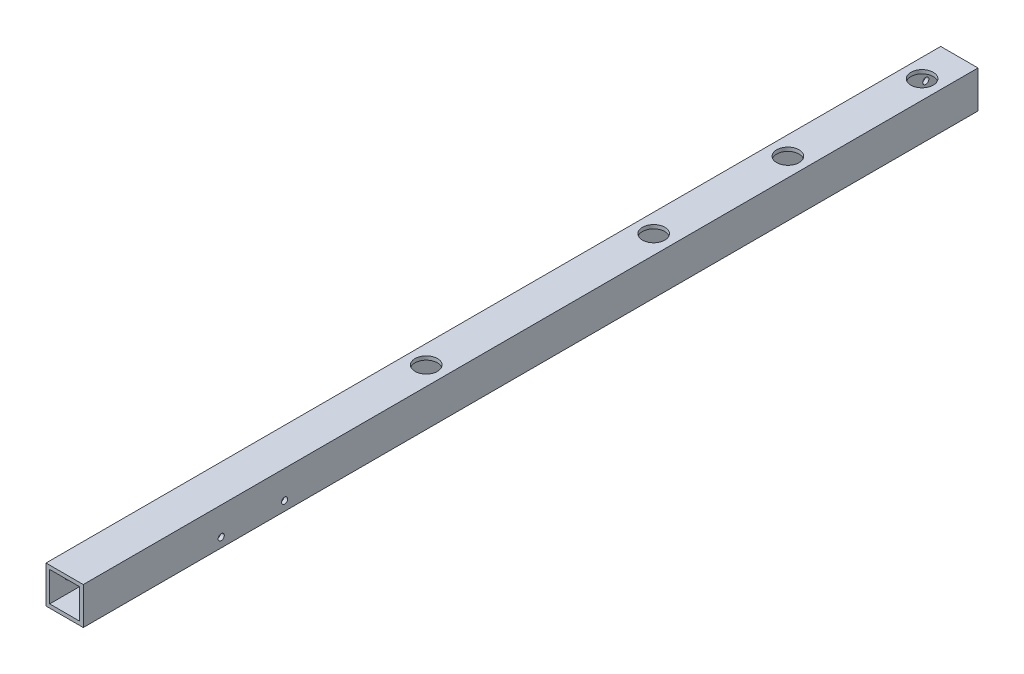
SolidWorks part; units mm, degrees
ref_plane "正面" through (0, 0, 0) normal (0, 0, 1) x (1, 0, 0)
ref_plane "平面" through (0, 0, 0) normal (0, 1, 0) x (1, 0, 0)
ref_plane "右側面" through (0, 0, 0) normal (1, 0, 0) x (0, 0, -1)
sketch "ｽｹｯﾁ1" plane through (0, 0, 0) normal (0, 0, 1) x (1, 0, 0)
  line L1 (-10, 10) -> (10, 10)
  line L2 (-10, 10) -> (-10, -10)
  line L3 (-10, -10) -> (10, -10)
  line L4 (10, 10) -> (10, -10)
  line L5 (-10, 10) -> (10, -10) construction
  line L6 (-10, -10) -> (10, 10) construction
  line L7 (-8, 8) -> (8, 8)
  line L8 (-8, 8) -> (-8, -8)
  line L9 (-8, -8) -> (8, -8)
  line L10 (8, 8) -> (8, -8)
  line L11 (-8, 8) -> (8, -8) construction
  line L12 (-8, -8) -> (8, 8) construction
  point P0 (0, 0)
  point P6 (0, 0)
  dimension "D1" = 20
  dimension "D2" = 20
  dimension "D3" = 16
  dimension "D4" = 16
extrude "ﾎﾞｽ - 押し出し1" add sketch "ｽｹｯﾁ1" along normal blind 560
sketch "ｽｹｯﾁ3" plane through (10, 0, 0) normal (1, 0, 0) x (0, 0, -1)
  line L0 (-560, 0) -> (-530, 0)
  line L1 (-560, -10) -> (-560, 10) construction
  line L2 (-530, 0) -> (-30, 0)
  circle A0 centre (-530, 0) radius 2.2
  circle A1 centre (-30, 0) radius 2.2
  dimension "D2" = 4.4
  dimension "D4" = 4.4
  dimension "D1" = 30
  dimension "D3" = 500
extrude "ｶｯﾄ - 押し出し2" cut sketch "ｽｹｯﾁ3" against normal blind 560
sketch "ｽｹｯﾁ4" plane through (0, 10, 0) normal (0, 1, 0) x (1, 0, 0)
  line L0 (0, -560) -> (0, -550)
  line L1 (10, -560) -> (-10, -560) construction
  line L2 (0, -550) -> (0, -10)
  circle A0 centre (0, -550) radius 2.2
  circle A1 centre (0, -10) radius 2.2
  dimension "D2" = 4.4
  dimension "D4" = 4.4
  dimension "D1" = 10
  dimension "D3" = 540
extrude "ｶｯﾄ - 押し出し3" cut sketch "ｽｹｯﾁ4" against normal blind 560
sketch "ｽｹｯﾁ6" plane through (0, 10, 0) normal (0, 1, 0) x (1, 0, 0)
  line L0 (0, -10) -> (0, -57)
  line L1 (0, -57) -> (0, -122)
  line L2 (0, -122) -> (0, -187)
  circle A0 centre (0, -57) radius 2.2
  circle A1 centre (0, -122) radius 2.2
  circle A2 centre (0, -187) radius 2.2
  dimension "D2" = 4.4
  dimension "D5" = 4.4
  dimension "D6" = 4.4
  dimension "D1" = 47
  dimension "D3" = 65
  dimension "D4" = 65
sketch "ｽｹｯﾁ7" plane through (0, 0, 0) normal (0, 0, -1) x (-1, 0, 0)
  line L1 (20.5547, -20.8177) -> (-20.5547, -20.8177)
  line L2 (20.5547, -20.8177) -> (20.5547, 20.8177)
  line L3 (20.5547, 20.8177) -> (-20.5547, 20.8177)
  line L4 (-20.5547, -20.8177) -> (-20.5547, 20.8177)
  line L5 (20.5547, -20.8177) -> (-20.5547, 20.8177) construction
  line L6 (20.5547, 20.8177) -> (-20.5547, -20.8177) construction
  point P0 (0, 0)
extrude "ｶｯﾄ - 押し出し7" cut sketch "ｽｹｯﾁ7" against normal blind 40
sketch "ｽｹｯﾁ8" plane through (0, 0, 560) normal (0, 0, 1) x (1, 0, 0)
  line L1 (26.7152, 16.8398) -> (-26.7152, 16.8398)
  line L2 (26.7152, 16.8398) -> (26.7152, -16.8398)
  line L3 (26.7152, -16.8398) -> (-26.7152, -16.8398)
  line L4 (-26.7152, 16.8398) -> (-26.7152, -16.8398)
  line L5 (26.7152, 16.8398) -> (-26.7152, -16.8398) construction
  line L6 (26.7152, -16.8398) -> (-26.7152, 16.8398) construction
  point P0 (0, 0)
extrude "ｶｯﾄ - 押し出し8" cut sketch "ｽｹｯﾁ8" against normal blind 40
sketch "ｽｹｯﾁ9" plane through (-10, 0, 0) normal (-1, 0, 0) x (0, 0, 1)
  line L0 (510, 0) -> (520, 0)
  line L2 (520, -10) -> (520, 10) construction
  line L3 (510, 0) -> (490, 0)
  circle A0 centre (510, 0) radius 1
  circle A1 centre (490, 0) radius 1
  dimension "D2" = 2
  dimension "D4" = 2
  dimension "D1" = 10
  dimension "D3" = 20
extrude "ｶｯﾄ - 押し出し9" cut sketch "ｽｹｯﾁ9" against normal blind 10
sketch "ｽｹｯﾁ10" plane through (-10, 0, 0) normal (-1, 0, 0) x (0, 0, 1)
  line L0 (40, 0) -> (50, 0)
  line L1 (40, -10) -> (40, 10) construction
  line L2 (50, 0) -> (70, 0)
  circle A0 centre (50, 0) radius 1
  circle A1 centre (70, 0) radius 1
  dimension "D2" = 2
  dimension "D4" = 2
  dimension "D1" = 10
  dimension "D3" = 20
extrude "ｶｯﾄ - 押し出し10" cut sketch "ｽｹｯﾁ10" against normal blind 10
sketch "ｽｹｯﾁ11" plane through (0, 10, 0) normal (0, 1, 0) x (1, 0, 0)
  line L0 (0, -40) -> (0, -60)
  line L1 (-10, -40) -> (10, -40) construction
  line L2 (0, -60) -> (0, -132)
  line L3 (0, -132) -> (0, -204)
  circle A0 centre (0, -60) radius 2.1
  circle A1 centre (0, -132) radius 2.1
  circle A3 centre (0, -204) radius 2.1
  dimension "D4" = 4.2
  dimension "D5" = 4.2
  dimension "D6" = 4.2
  dimension "D1" = 20
  dimension "D2" = 72
  dimension "D3" = 72
extrude "ｶｯﾄ - 押し出し11" cut sketch "ｽｹｯﾁ11" against normal through all
sketch "ｽｹｯﾁ12" plane through (0, 10, 0) normal (0, 1, 0) x (1, 0, 0)
  circle A0 centre (0, -60) radius 6
  circle A1 centre (0, -132) radius 6
  circle A2 centre (0, -204) radius 6
  dimension "D1" = 12
  dimension "D2" = 12
  dimension "D3" = 12
extrude "ｶｯﾄ - 押し出し12" cut sketch "ｽｹｯﾁ12" against normal blind 10
sketch "ｽｹｯﾁ13" plane through (-10, 0, 0) normal (-1, 0, 0) x (0, 0, 1)
  line L4 (131, 10) -> (131, 5)
  line L5 (520, 10) -> (40, 10) construction
  line L6 (131, 5) -> (114, 5)
  line L7 (131, 5) -> (148, 5)
  circle A2 centre (148, 5) radius 2.1
  circle A3 centre (114, 5) radius 2.1
  dimension "D5" = 4.2
  dimension "D6" = 4.2
  dimension "D1" = 5
  dimension "D2" = 17
  dimension "D3" = 17
sketch "ｽｹｯﾁ14" plane through (-10, 0, 0) normal (-1, 0, 0) x (0, 0, 1)
  line L2 (429, -10) -> (429, -5)
  line L3 (520, -10) -> (40, -10) construction
  line L4 (429, -5) -> (446, -5)
  line L5 (429, -5) -> (412, -5)
  circle A0 centre (446, -5) radius 2.1
  circle A1 centre (412, -5) radius 2.1
  dimension "D4" = 4.2
  dimension "D5" = 4.2
  dimension "D1" = 5
  dimension "D2" = 17
  dimension "D3" = 17
sketch "ｽｹｯﾁ15" plane through (0, 10, 0) normal (0, 1, 0) x (1, 0, 0)
  line L0 (0, -520) -> (0, -326)
  line L1 (-10, -520) -> (10, -520) construction
  circle A0 centre (0, -326) radius 2.1
  dimension "D2" = 4.2
  dimension "D1" = 194
extrude "ｶｯﾄ - 押し出し16" cut sketch "ｽｹｯﾁ15" against normal through all
sketch "ｽｹｯﾁ16" plane through (0, 10, 0) normal (0, 1, 0) x (1, 0, 0)
  circle A0 centre (0, -326) radius 6
  dimension "D1" = 12
extrude "ｶｯﾄ - 押し出し17" cut sketch "ｽｹｯﾁ16" against normal blind 10
hole_wizard "M4x0.7 ねじ穴6" positions "3Dｽｹｯﾁ7" profile "ｽｹｯﾁ23" tap size "M4x0.7" standard "JIS"
sketch3d "3Dｽｹｯﾁ7"
  line L0 (-8, 0, 70) -> (-10, 0, 70) construction
  line L1 (-8, 0, 50) -> (-10, 0, 50) construction
  point P0 (-10, 0, 70)
  point P4 (-10, 0, 50)
sketch "ｽｹｯﾁ23" plane through (-10, 0, 70) normal (0, 1, 0) x (0, 0, 1)
  line L0 (0, 0) -> (0, 12.4914)
  line L1 (0, 12.4914) -> (1.65, 11.5)
  line L2 (1.65, 11.5) -> (1.65, 0)
  line L5 (1.65, 0) -> (0, 0)
  line L10 (0, 12.4914) -> (-1.65, 11.5) construction
  line L11 (0, -6.35) -> (0, 107.95) construction
  dimension "ねじ下穴ﾄﾞﾘﾙ直径" = 3.3
  dimension "ねじ下穴ﾄﾞﾘﾙの深さ" = 11.5
  dimension "ﾄﾞﾘﾙ角度" = 118
cosmetic thread "穴のねじ山12" parameters "D1"=2, "D2"=4
cosmetic thread "穴のねじ山13" parameters "D1"=2, "D2"=4
hole_wizard "M4x0.7 ねじ穴7" positions "3Dｽｹｯﾁ8" profile "ｽｹｯﾁ24" tap size "M4x0.7" standard "JIS"
sketch3d "3Dｽｹｯﾁ8"
  line L0 (-8, 0, 490) -> (-10, 0, 490) construction
  line L1 (-8, 0, 510) -> (-10, 0, 510) construction
  point P0 (-8, 0, 490)
  point P4 (-10, 0, 510)
sketch "ｽｹｯﾁ24" plane through (-8, 0, 490) normal (0, 1, 0) x (0, 0, -1)
  line L0 (0, 0) -> (0, 12.4914)
  line L1 (0, 12.4914) -> (1.65, 11.5)
  line L2 (1.65, 11.5) -> (1.65, 0)
  line L5 (1.65, 0) -> (0, 0)
  line L10 (0, 12.4914) -> (-1.65, 11.5) construction
  line L11 (0, -6.35) -> (0, 107.95) construction
  dimension "ねじ下穴ﾄﾞﾘﾙ直径" = 3.3
  dimension "ねじ下穴ﾄﾞﾘﾙの深さ" = 11.5
  dimension "ﾄﾞﾘﾙ角度" = 118
cosmetic thread "穴のねじ山14" parameters "D1"=2, "D2"=4
cosmetic thread "穴のねじ山15" parameters "D1"=2, "D2"=4
sketch "ｽｹｯﾁ26" plane through (10, 0, 0) normal (1, 0, 0) x (0, 0, -1)
  line L0 (-520, -10) -> (-520, -5)
  line L1 (-520, 10) -> (-520, -10) construction
  line L2 (-520, -5) -> (-446, -5)
  line L3 (-446, -5) -> (-412, -5)
  circle A0 centre (-446, -5) radius 1
  circle A1 centre (-412, -5) radius 1
  dimension "D4" = 2
  dimension "D5" = 2
  dimension "D1" = 74
  dimension "D2" = 34
  dimension "D3" = 5
extrude "ｶｯﾄ - 押し出し18" cut sketch "ｽｹｯﾁ26" against normal blind 10
hole_wizard "M4x0.7 ねじ穴9" positions "3Dｽｹｯﾁ10" profile "ｽｹｯﾁ28" tap size "M4x0.7" standard "JIS"
sketch3d "3Dｽｹｯﾁ10"
  line L0 (8, -5, 446) -> (10, -5, 446) construction
  line L1 (8, -5, 412) -> (10, -5, 412) construction
  point P0 (10, -5, 446)
  point P4 (10, -5, 412)
sketch "ｽｹｯﾁ28" plane through (10, -5, 446) normal (0, 1, 0) x (0, 0, -1)
  line L0 (0, 0) -> (0, 12.4914)
  line L1 (0, 12.4914) -> (1.65, 11.5)
  line L2 (1.65, 11.5) -> (1.65, 0)
  line L5 (1.65, 0) -> (0, 0)
  line L10 (0, 12.4914) -> (-1.65, 11.5) construction
  line L11 (0, -6.35) -> (0, 107.95) construction
  dimension "ねじ下穴ﾄﾞﾘﾙ直径" = 3.3
  dimension "ねじ下穴ﾄﾞﾘﾙの深さ" = 11.5
  dimension "ﾄﾞﾘﾙ角度" = 118
cosmetic thread "穴のねじ山18" parameters "D1"=2, "D2"=4
cosmetic thread "穴のねじ山19" parameters "D1"=2, "D2"=4
